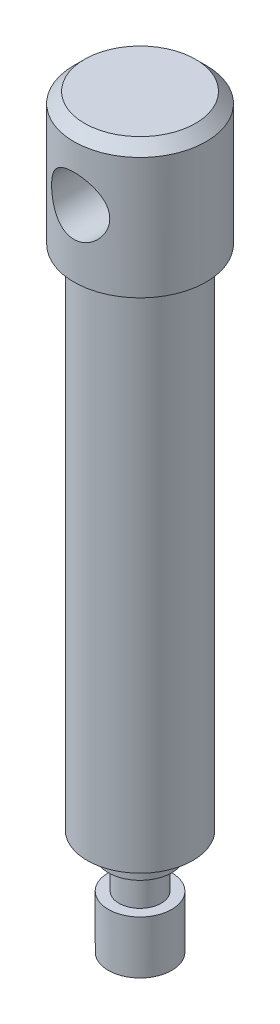
SolidWorks part; units mm, degrees
material "AISI 1045 Aço, trefilado"
ref_plane "Front" through (0, 0, 0) normal (0, 0, 1) x (1, 0, 0)
ref_plane "Top" through (0, 0, 0) normal (0, 1, 0) x (1, 0, 0)
ref_plane "Right" through (0, 0, 0) normal (1, 0, 0) x (0, 0, -1)
sketch "Sketch1" plane through (0, 0, 0) normal (0, 0, 1) x (1, 0, 0)
  line L0 (0, 0) -> (0, 167.1475) construction
  line L1 (0, 0) -> (6, 3.4641)
  line L2 (6, 3.4641) -> (6, 13.4641)
  line L3 (6, 13.4641) -> (4, 13.4641)
  line L4 (4, 13.4641) -> (4, 19.4641)
  line L5 (4, 19.4641) -> (6, 19.4641)
  line L6 (6, 19.4641) -> (6, 23.4641)
  line L7 (6, 23.4641) -> (10, 23.4641)
  line L8 (10, 23.4641) -> (10, 119.4641)
  line L9 (10, 119.4641) -> (12.5, 119.4641)
  line L10 (12.5, 119.4641) -> (12.5, 144.4641)
  line L11 (12.5, 144.4641) -> (0, 144.4641)
  line L12 (0, 144.4641) -> (0, 0)
  dimension "D1" = 12
  dimension "D2" = 10
  dimension "D3" = 4
  dimension "D4" = 96
  dimension "D5" = 25
  dimension "D6" = 60
  dimension "D7" = 25
  dimension "D8" = 20
  dimension "D9" = 6
  dimension "D10" = 4
revolve "Revolve1" add sketch "Sketch1" angle 360 about L0
sketch "Sketch2" plane through (0, 0, 0) normal (0, 0, 1) x (1, 0, 0)
  line L0 (12.5, 144.4641) -> (-12.5, 144.4641) construction
  circle A0 centre (0, 131.9641) radius 5.5
  dimension "D1" = 11
  dimension "D2" = 12.5
extrude "Cut-Extrude1" cut sketch "Sketch2" against normal through all and the other way through all
chamfer "Chamfer1" distance 2 angle 45
